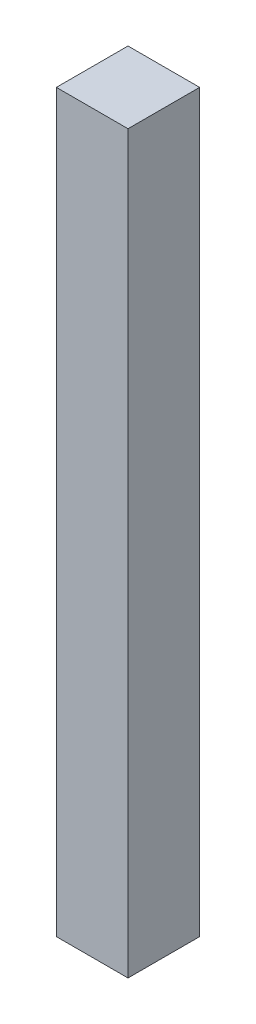
SolidWorks part; units mm, degrees
ref_plane "Front Plane" through (0, 0, 0) normal (0, 0, 1) x (1, 0, 0)
ref_plane "Top Plane" through (0, 0, 0) normal (0, 1, 0) x (1, 0, 0)
ref_plane "Right Plane" through (0, 0, 0) normal (1, 0, 0) x (0, 0, -1)
sketch "Sketch1" plane through (0, 0, 0) normal (0, 1, 0) x (1, 0, 0)
  line L1 (-39.8355, 18.6136) -> (-14.4355, 18.6136)
  line L2 (-39.8355, 18.6136) -> (-39.8355, -6.7864)
  line L3 (-39.8355, -6.7864) -> (-14.4355, -6.7864)
  line L4 (-14.4355, 18.6136) -> (-14.4355, -6.7864)
  dimension "D1" = 25.4
  dimension "D2" = 25.4
extrude "Boss-Extrude1" add sketch "Sketch1" along normal blind 260.8
